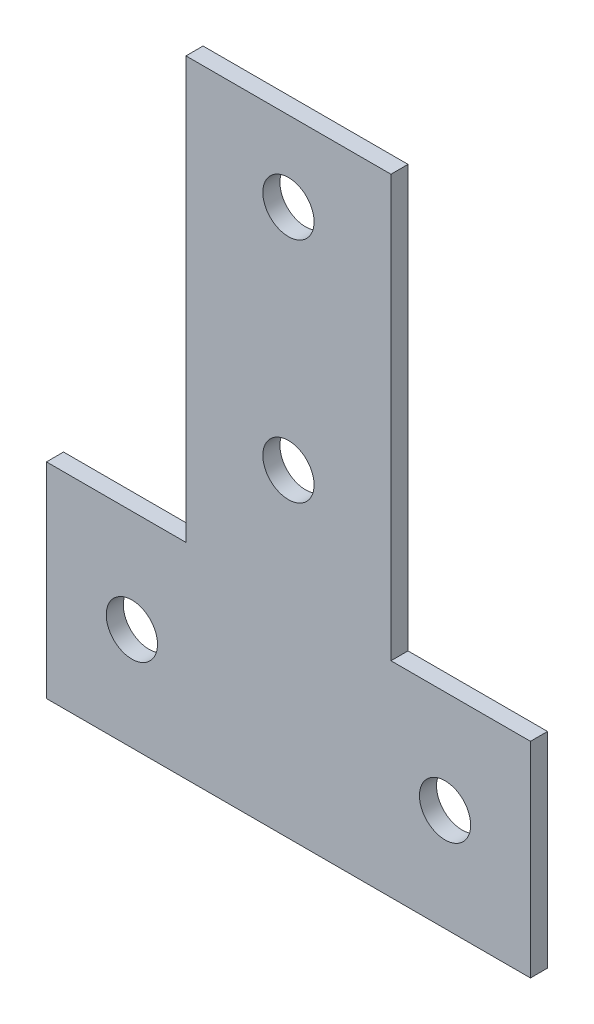
SolidWorks part; units mm, degrees
ref_plane "Спереди" through (0, 0, 0) normal (0, 0, 1) x (1, 0, 0)
ref_plane "Сверху" through (0, 0, 0) normal (0, 1, 0) x (1, 0, 0)
ref_plane "Справа" through (0, 0, 0) normal (1, 0, 0) x (0, 0, -1)
sketch "Эскиз1" plane through (0, 0, 0) normal (0, 0, 1) x (1, 0, 0)
  line L0 (-42.5, 0) -> (42.5, 0)
  line L1 (-42.5, 0) -> (-42.5, 36)
  line L2 (-42.5, 36) -> (-18, 36)
  line L3 (-18, 36) -> (-18, 110)
  line L4 (-18, 110) -> (18, 110)
  line L5 (18, 110) -> (18, 36)
  line L6 (18, 36) -> (42.5, 36)
  line L7 (42.5, 36) -> (42.5, 0)
  line L8 (-27.5, 18) -> (27.5, 18) construction
  circle A0 centre (0, 96) radius 4.5
  circle A1 centre (0, 56) radius 4.5
  circle A2 centre (-27.5, 18) radius 4.5
  circle A3 centre (27.5, 18) radius 4.5
  point P4 (0, 0)
  point P18 (0, 18)
  point P19 (42.5, 18)
  dimension "D5" = 14
  dimension "D6" = 40
  dimension "D7" = 9
  dimension "D1" = 85
  dimension "D2" = 110
  dimension "D3" = 36
  dimension "D4" = 55
extrude "Бобышка-Вытянуть1" add sketch "Эскиз1" along normal blind 3
